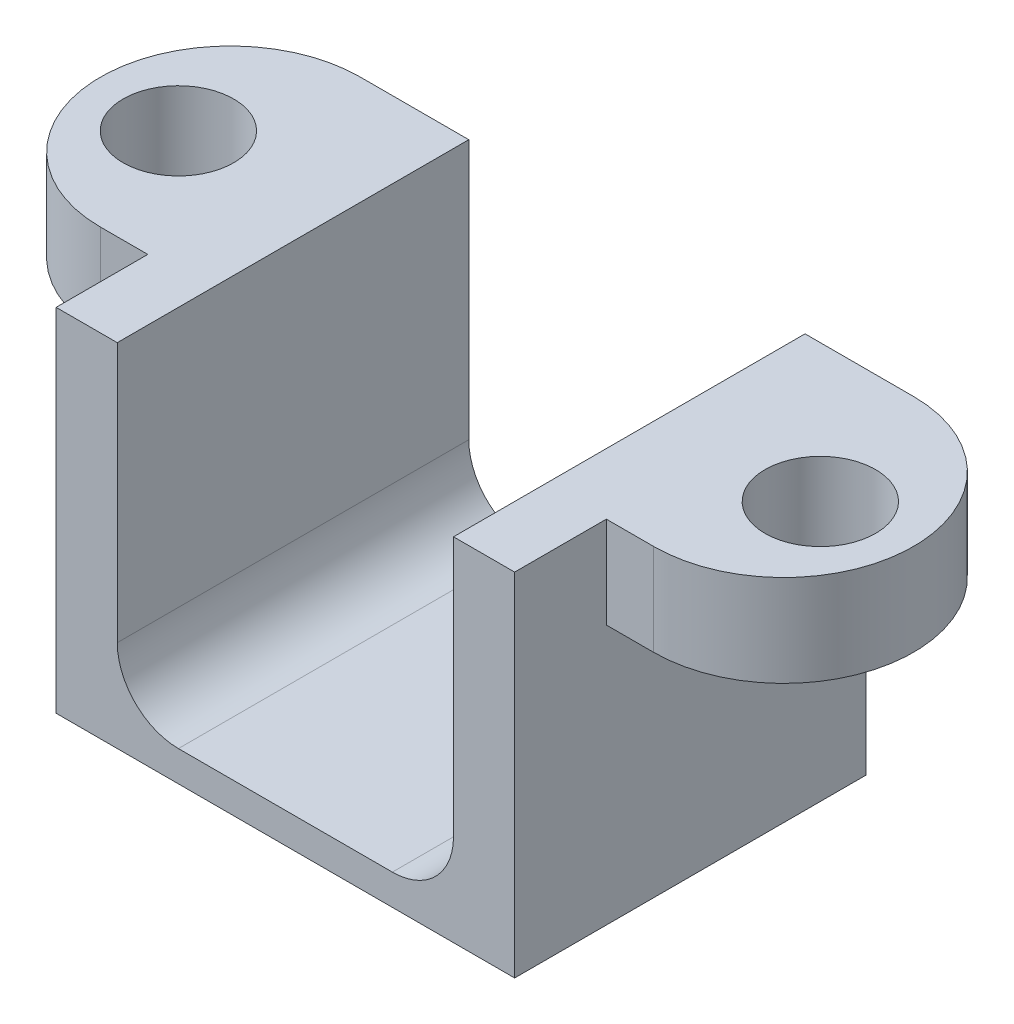
SolidWorks part; units mm, degrees
ref_plane "Front Plane" through (0, 0, 0) normal (0, 0, 1) x (1, 0, 0)
ref_plane "Top Plane" through (0, 0, 0) normal (0, 1, 0) x (1, 0, 0)
ref_plane "Right Plane" through (0, 0, 0) normal (1, 0, 0) x (0, 0, -1)
sketch "Sketch1" plane through (0, 0, 0) normal (0, 0, 1) x (1, 0, 0)
  line L1 (0, 0) -> (15, 0)
  line L2 (0, 0) -> (0, 11.5)
  line L3 (0, 11.5) -> (15, 11.5)
  line L4 (15, 0) -> (15, 11.5)
  dimension "D1" = 11.5
  dimension "D2" = 15
extrude "Boss-Extrude1" add sketch "Sketch1" along normal blind 11.5
sketch "Sketch3" plane through (0, 0, 11.5) normal (0, 0, 1) x (1, 0, 0)
  line L0 (15, 11.5) -> (0, 11.5) construction
  line L1 (2, 11.5) -> (13, 11.5)
  line L2 (2, 11.5) -> (2, 1)
  line L3 (2, 1) -> (13, 1)
  line L4 (13, 11.5) -> (13, 1)
  dimension "D1" = 2
  dimension "D2" = 2
  dimension "D3" = 10.5
extrude "Cut-Extrude1" cut sketch "Sketch3" against normal blind 11.5
fillet "Fillet1" radius 2 2 edges at (13, 1, 5.75) (2, 1, 5.75)
sketch "Sketch4" plane through (0, 11.5, 0) normal (0, 1, 0) x (1, 0, 0)
  line L1 (0, 0) -> (-1.55, 0)
  line L2 (0, 0) -> (0, -8.5)
  line L3 (0, -8.5) -> (-1.55, -8.5)
  line L5 (15, 0) -> (16.55, 0)
  line L6 (15, 0) -> (15, -8.5)
  line L7 (15, -8.5) -> (16.55, -8.5)
  arc A0 (-1.55, 0) -> (-1.55, -8.5) centre (-1.55, -4.25) ccw
  arc A1 (16.55, 0) -> (16.55, -8.5) centre (16.55, -4.25) cw
  dimension "D1" = 8.5
  dimension "D2" = 1.55
  dimension "D3" = 1.55
  dimension "D4" = 8.5
extrude "Boss-Extrude2" add sketch "Sketch4" against normal blind 3
sketch "Sketch5" plane through (0, 11.5, 0) normal (0, 1, 0) x (1, 0, 0)
  line L0 (2, 0) -> (-1.55, 0) construction
  line L1 (2, 0) -> (2, -11.5) construction
  circle A0 centre (-3, -4.5) radius 1.8092
  dimension "D1" = 4.5
  dimension "D2" = 5
extrude "Cut-Extrude2" cut sketch "Sketch5" against normal blind 3
ref_plane "Plane1" through (7.5, 0, 0) normal (-1, 0, 0) x (0, 0, 1)
mirror "Mirror1" about plane through (7.5, 0, 0) normal (-1, 0, 0) of "Cut-Extrude2"
